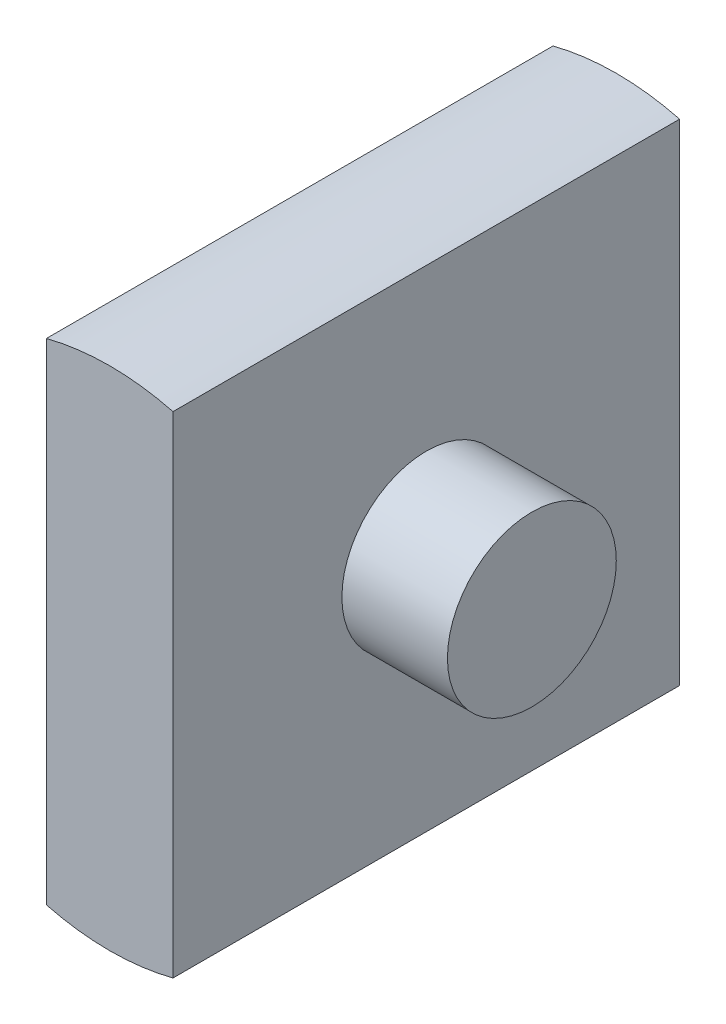
SolidWorks part; units mm, degrees
ref_plane "Front Plane" through (0, 0, 0) normal (0, 0, 1) x (1, 0, 0)
ref_plane "Top Plane" through (0, 0, 0) normal (0, 1, 0) x (1, 0, 0)
ref_plane "Right Plane" through (0, 0, 0) normal (1, 0, 0) x (0, 0, -1)
sketch "sketch1_tool_base" plane through (0, 0, 0) normal (0, 0, 1) x (1, 0, 0)
  line L0 (0, 0) -> (-7.5, 29.0474) construction
  line L5 (0, 0) -> (7.5, -29.0474) construction
  line L6 (-7.5, 29.0474) -> (-7.5, -29.0474)
  line L7 (7.5, 29.0474) -> (7.5, -29.0474)
  arc A1 (7.5, 29.0474) -> (-7.5, 29.0474) centre (0, 0) ccw
  arc A2 (-7.5, -29.0474) -> (7.5, -29.0474) centre (0, 0) ccw
  dimension "D1" = 15
  dimension "D3" = 30
extrude "Boss-Extrude1" add sketch "sketch1_tool_base" along normal blind 60
sketch "sketch2_tool_base" plane through (0, 0, 0) normal (1, 0, 0) x (0, 0, -1)
  line L0 (0, 0) -> (-60, 0) construction
  line L1 (-60, -29.0474) -> (-60, 29.0474) construction
  circle A2 centre (-30, 0) radius 10
  dimension "D1" = 20
extrude "Boss-Extrude2" add sketch "sketch2_tool_base" along normal mid plane 40
